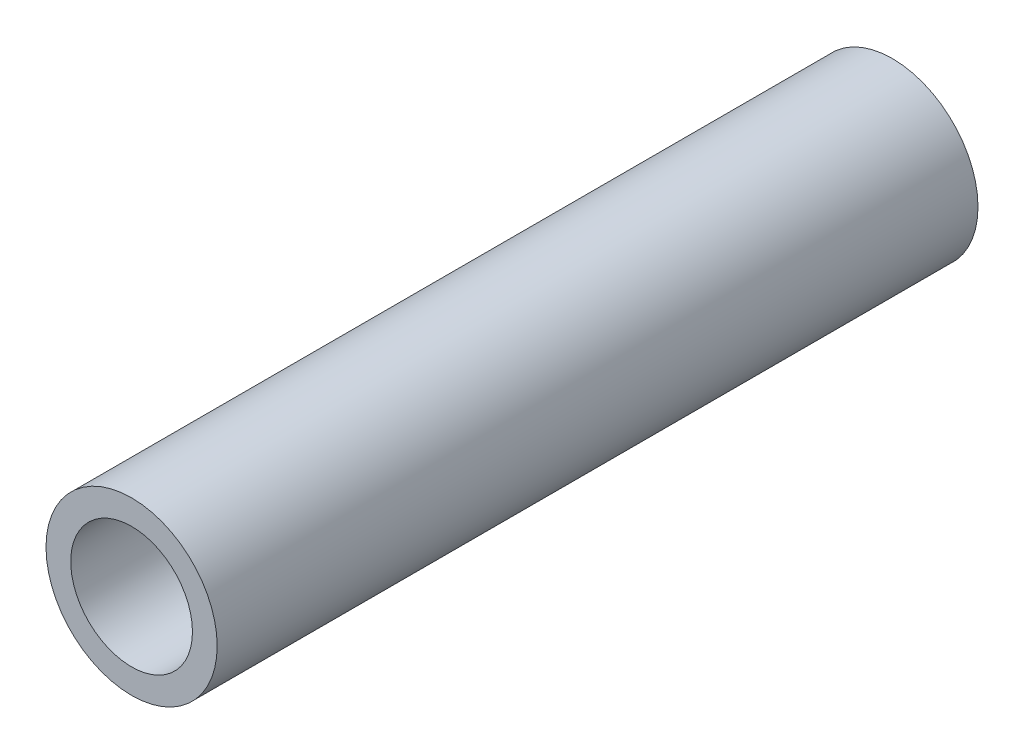
SolidWorks part; units mm, degrees
ref_plane "Front Plane" through (0, 0, 0) normal (0, 0, 1) x (1, 0, 0)
ref_plane "Top Plane" through (0, 0, 0) normal (0, 1, 0) x (1, 0, 0)
ref_plane "Right Plane" through (0, 0, 0) normal (1, 0, 0) x (0, 0, -1)
sketch "Sketch1" plane through (0, 0, 0) normal (0, 0, 1) x (1, 0, 0)
  circle A0 centre (0, 0) radius 2.25
  circle A1 centre (0, 0) radius 1.6
  dimension "OD" = 4.5
  dimension "ID" = 3.2
extrude "Extrude1" add sketch "Sketch1" along normal mid plane 20
sketch "Sketch2" plane through (0, 0, 0) normal (1, 0, 0) x (0, 0, -1)
  line L0 (-10, -1.6) -> (10, -1.6) construction
  line L3 (10, 1.6) -> (-10, 1.6) construction
  line L5 (-10, -1.6) -> (10, -1.6)
  line L6 (10, 1.6) -> (-10, 1.6)
sketch "Sketch4" plane through (0, 0, 10) normal (0, 0, 1) x (1, 0, 0)
  line L0 (0, 0) -> (-1.1314, 1.1314)
  line L1 (0, -2.475) -> (0, 2.475) construction
  circle A0 centre (0, 0) radius 1.6 construction
  dimension "D1" = 45
